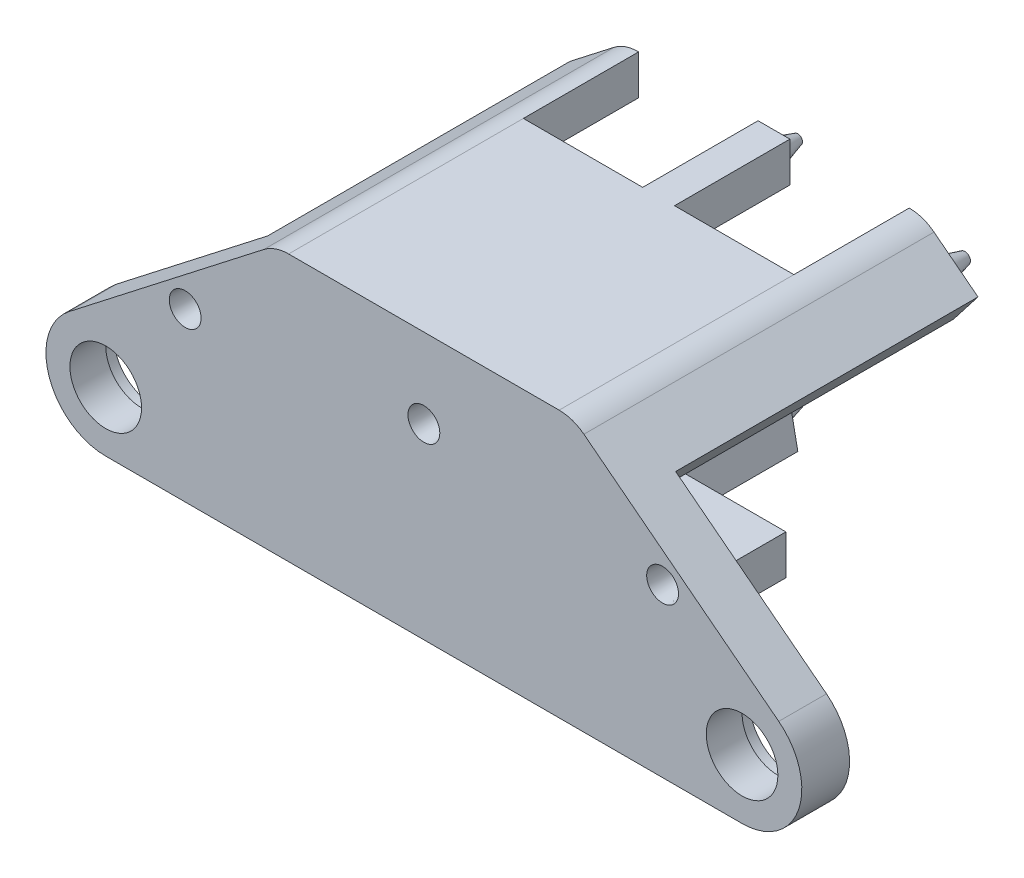
SolidWorks part; units mm, degrees
ref_plane "Front Plane" through (0, 0, 0) normal (0, 0, 1) x (1, 0, 0)
ref_plane "Top Plane" through (0, 0, 0) normal (0, 1, 0) x (1, 0, 0)
ref_plane "Right Plane" through (0, 0, 0) normal (1, 0, 0) x (0, 0, -1)
sketch "Sketch1" plane through (0, 0, 0) normal (0, 0, 1) x (1, 0, 0)
  line L0 (-44.5991, 4.9244) -> (-20.1116, 23.934)
  line L3 (17, 25) -> (-17, 25)
  line L9 (44.5991, 4.9244) -> (20.1116, 23.934)
  line L10 (0, 26.7904) -> (0, -38.8482) construction
  line L14 (-40, -8.5) -> (40, -8.5)
  arc A0 (-44.5991, 4.9244) -> (-40, -8.5) centre (-40, -1) ccw
  arc A1 (44.5991, 4.9244) -> (40, -8.5) centre (40, -1) cw
  arc A2 (20.1116, 23.934) -> (17, 25) centre (17, 19.9257) ccw
  arc A3 (-17, 25) -> (-20.1116, 23.934) centre (-17, 19.9257) ccw
  point P0 (0, 0)
  point P3 (0, 25)
  point P7 (0, -8.5)
  dimension "D3" = 7.5
  dimension "D1" = 34
  dimension "D4" = 7.5
  dimension "D5" = 25
  dimension "D6" = 31
  dimension "D9" = 5.0743
  dimension "D12" = 5.0743
  dimension "D2" = 80
  dimension "D7" = 31
  dimension "D8" = 8.5
  dimension "D10" = 40
  dimension "D11" = 7.5
extrude "Boss-Extrude2" add sketch "Sketch1" along normal mid plane 6
sketch "Sketch3" plane through (0, 0, -3) normal (0, 0, -1) x (-1, 0, 0)
  circle A1 centre (-39.9875, -1) radius 4.5
  dimension "D1" = 9
  dimension "D2" = 40
  dimension "D3" = 7.5
extrude "Cut-Extrude3" cut sketch "Sketch3" against normal blind 8
sketch "Sketch4" plane through (0, 0, -3) normal (0, 0, -1) x (-1, 0, 0)
  circle A0 centre (-39.9875, -1) radius 5
  dimension "D1" = 10
extrude "Cut-Extrude4" cut sketch "Sketch4" against normal blind 1.5
mirror "Mirror1" about plane through (0, 0, 0) normal (1, 0, 0) of "Cut-Extrude3", "Cut-Extrude4"
sketch "Sketch5" plane through (0, 0, -3) normal (0, 0, -1) x (-1, 0, 0)
  line L0 (-17, 25) -> (17, 25) construction
  line L1 (-17, 25) -> (17, 25)
  line L2 (-17, 25) -> (-17, 20)
  line L3 (-17, 20) -> (-2, 20)
  line L4 (17, 25) -> (17, 20)
  line L5 (40, -8.5) -> (-40, -8.5) construction
  line L7 (-2, 20) -> (-2, -3.5)
  line L9 (2, 20) -> (2, -3.5)
  line L10 (2, 20) -> (17, 20)
  line L11 (16, -8.5) -> (-16, -8.5)
  line L12 (16, -8.5) -> (16, -3.5)
  line L13 (16, -3.5) -> (2, -3.5)
  line L14 (-16, -8.5) -> (-16, -3.5)
  line L15 (-2, -3.5) -> (-16, -3.5)
  point P9 (-17, 22.5)
  dimension "D1" = 34
  dimension "D2" = 5
  dimension "D3" = 4
  dimension "D4" = 5
  dimension "D5" = 32
  dimension "D6" = 2
  dimension "D7" = 16
  dimension "D8" = 17
extrude "Boss-Extrude3" add sketch "Sketch5" along normal blind 20.5
sketch "Sketch7" plane through (0, 0, -3) normal (0, 0, -1) x (-1, 0, 0)
  line L0 (17, 20) -> (22.575, 15.6919)
  line L1 (22.575, 15.6919) -> (25.6411, 19.6415)
  line L2 (20.1116, 23.934) -> (44.5991, 4.9244) construction
  line L3 (25.6411, 19.6415) -> (20.1116, 23.934)
  line L4 (17, 20) -> (17, 25) construction
  line L5 (17, 20) -> (17, 25)
  arc A1 (20.1116, 23.934) -> (17, 25) centre (17, 19.9257) ccw construction
  arc A2 (20.1116, 23.934) -> (17, 25) centre (17, 19.9257) ccw
  dimension "D1" = 7
  dimension "D2" = 5
extrude "Boss-Extrude4" add sketch "Sketch7" along normal blind 38
mirror "Mirror2" about plane through (0, 0, 0) normal (1, 0, 0) of "Boss-Extrude4"
sketch "Sketch8" plane through (0, 0, -23.5) normal (0, 0, -1) x (-1, 0, 0)
  line L0 (0, -8.5) -> (3, -8.5)
  line L1 (-16, -8.5) -> (16, -8.5) construction
  line L2 (3, -8.5) -> (2, -3.5)
  line L3 (2, -3.5) -> (-2, -3.5)
  line L4 (-2, -3.5) -> (-3, -8.5)
  line L5 (-3, -8.5) -> (0, -8.5)
  dimension "D1" = 3
  dimension "D2" = 3
extrude "Boss-Extrude5" add sketch "Sketch8" along normal up to surface (17.5 mm away) up to face at (-20.4833, 20.9053, -41)
sketch "Sketch10" plane through (0, 0, -41) normal (0, 0, -1) x (-1, 0, 0)
  line L0 (25.6411, 19.6415) -> (20.1116, 23.934) construction
  line L1 (2, -3.5) -> (-2, -3.5) construction
  line L2 (-3, -8.5) -> (3, -8.5) construction
  circle A0 centre (21, 20.0795) radius 1.5
  circle A1 centre (0, -6) radius 1.5
  dimension "D1" = 3
  dimension "D3" = 3
  dimension "D2" = 2.5
  dimension "D4" = 2.5
  dimension "D5" = 2.5
  dimension "D6" = 21
extrude "Boss-Extrude6" add sketch "Sketch10" along normal blind 3 draft 15
mirror "Mirror3" about plane through (0, 0, 0) normal (1, 0, 0) of "Boss-Extrude6"
sketch "Sketch11" plane through (0, 0, 3) normal (0, 0, 1) x (1, 0, 0)
  line L0 (17, 25) -> (-17, 25) construction
  circle A0 centre (0, 15) radius 2
  circle A1 centre (30, 12.5) radius 2
  circle A2 centre (-30, 12.5) radius 2
  dimension "D1" = 4
  dimension "D4" = 4
  dimension "D2" = 10
  dimension "D3" = 2.5
  dimension "D5" = 30
  dimension "D6" = 30
extrude "Cut-Extrude6" cut sketch "Sketch11" against normal blind 3 draft 6
sketch "Sketch12" plane through (0, 0, -23.5) normal (0, 0, -1) x (-1, 0, 0)
  line L0 (-16, -8.5) -> (-3, -8.5) construction
  line L1 (-16, -3.5) -> (-3.2, -3.5)
  line L2 (-16, -3.5) -> (-16, -8.5)
  line L3 (-16, -8.5) -> (-3.2, -8.5)
  line L4 (-3.2, -3.5) -> (-3.2, -8.5)
  dimension "D1" = 3.2
extrude "Boss-Extrude11" add sketch "Sketch12" along normal blind 3
mirror "Mirror4" about plane through (0, 0, 0) normal (1, 0, 0) of "Boss-Extrude11"
sketch "Sketch13" plane through (0, 0, -23.5) normal (0, 0, -1) x (-1, 0, 0)
  line L1 (-17, 25) -> (17, 25)
  line L2 (-17, 25) -> (-17, 20)
  line L3 (-17, 20) -> (17, 20)
  line L4 (17, 25) -> (17, 20)
extrude "Boss-Extrude12" add sketch "Sketch13" along normal blind 3
sketch "Sketch9" plane through (0, 0, -23.5) normal (0, 0, -1) x (-1, 0, 0)
  line L0 (-16, -3.5) -> (-16, -8.5) construction
  line L1 (-3.2, -8.5) -> (-3, -8.5) construction
  line L3 (0, 18.425) -> (0, -18.425) construction
  circle A0 centre (-9.85, -6) radius 1
  circle A1 centre (-9.85, 22.2) radius 1
  circle A2 centre (9.85, 22.2) radius 1
  circle A3 centre (9.85, -6) radius 1
  dimension "D4" = 2
  dimension "D5" = 2
  dimension "D1" = 6.15
  dimension "D2" = 2.5
  dimension "D3" = 28.2
extrude "Cut-Extrude5" cut sketch "Sketch9" along normal blind 5
sketch "Sketch15" plane through (0, -8.5, 0) normal (0, -1, 0) x (1, 0, 0)
  line L0 (-16, -26.5) -> (-16, -3) construction
  line L1 (-11.85, -14.57) -> (-7.85, -14.57)
  line L2 (-11.85, -14.57) -> (-11.85, -17.07)
  line L3 (-11.85, -17.07) -> (-7.85, -17.07)
  line L4 (-7.85, -14.57) -> (-7.85, -17.07)
  line L5 (7.85, -14.57) -> (11.85, -14.57)
  line L6 (7.85, -14.57) -> (7.85, -17.07)
  line L7 (7.85, -17.07) -> (11.85, -17.07)
  line L8 (11.85, -14.57) -> (11.85, -17.07)
  line L9 (-16, -26.5) -> (-3.2, -26.5) construction
  line L10 (16, -26.5) -> (3.2, -26.5) construction
  line L11 (16, -26.5) -> (16, -3) construction
  point P14 (11.85, -15.82)
  dimension "D1" = 4
  dimension "D2" = 2.5
  dimension "D3" = 4.15
  dimension "D4" = 9.43
  dimension "D5" = 9.43
  dimension "D6" = 4.15
  dimension "D7" = 2.5
  dimension "D8" = 4
extrude "Cut-Extrude7" cut sketch "Sketch15" against normal blind 10
sketch "Sketch16" plane through (0, 0, -26.5) normal (0, 0, -1) x (-1, 0, 0)
  line L0 (-17, 20) -> (17, 20) construction
  line L1 (-2, 20) -> (2, 20)
  line L2 (-2, 20) -> (-2, 25)
  line L3 (-2, 25) -> (2, 25)
  line L4 (2, 20) -> (2, 25)
  line L5 (17, 25) -> (-17, 25) construction
  point P8 (0, 20)
  dimension "D1" = 4
extrude "Boss-Extrude13" add sketch "Sketch16" along normal up to surface (14.5 mm away) up to face at (-1.5, -6, -41)
sketch "Sketch17" plane through (0, 0, -41) normal (0, 0, -1) x (-1, 0, 0)
  line L0 (2, 25) -> (-2, 25) construction
  line L1 (2, 20) -> (2, 25) construction
  circle A0 centre (0, 22.5) radius 1.5
  dimension "D1" = 3
  dimension "D2" = 2.5
  dimension "D3" = 2
extrude "Boss-Extrude14" add sketch "Sketch17" along normal up to surface (3 mm away) draft 17
